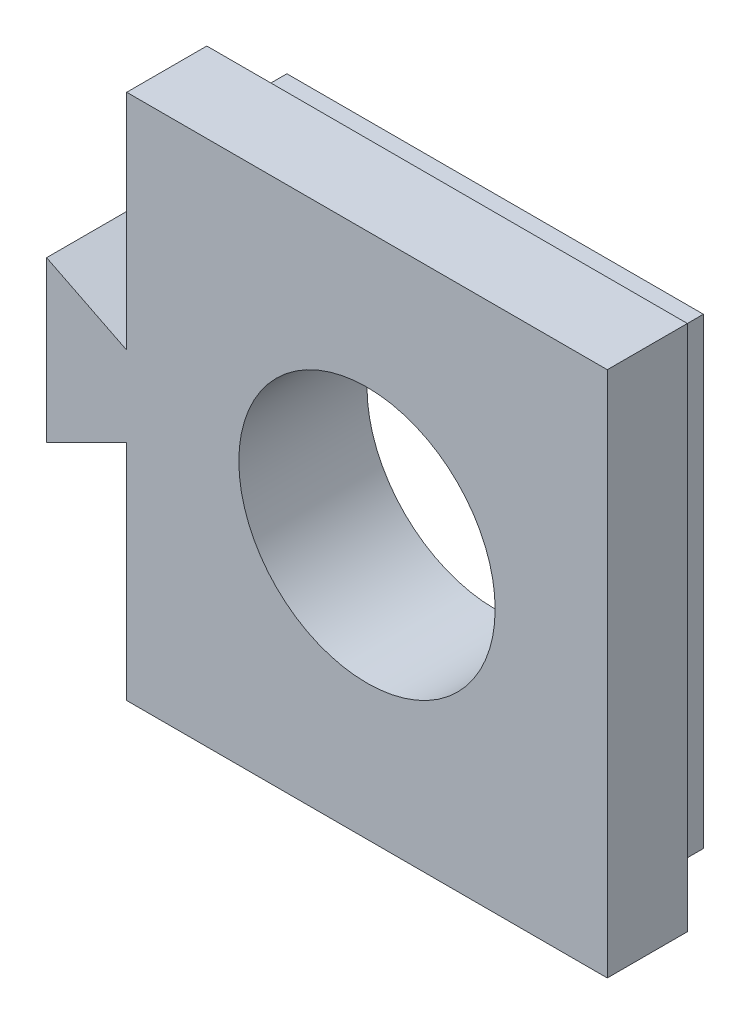
SolidWorks part; units mm, degrees
ref_plane "Alzado" through (0, 0, 0) normal (0, 0, 1) x (1, 0, 0)
ref_plane "Planta" through (0, 0, 0) normal (0, 1, 0) x (1, 0, 0)
ref_plane "Vista lateral" through (0, 0, 0) normal (1, 0, 0) x (0, 0, -1)
sketch "Croquis1" plane through (0, 0, 0) normal (0, 0, 1) x (1, 0, 0)
  line L1 (-2, -5.2848) -> (24, -5.2848)
  line L2 (-2, -5.2848) -> (-2, 23.6)
  line L3 (-2, 23.6) -> (24, 23.6)
  line L4 (24, -5.2848) -> (24, 23.6)
  circle A0 centre (11, 9.1576) radius 8
extrude "Saliente-Extruir1" add sketch "Croquis1" along normal blind 3
sketch "Croquis2" plane through (0, 0, 3) normal (0, 0, 1) x (1, 0, 0)
  line L8 (-4, 25.6) -> (-4, -7.2848)
  line L9 (26, 25.6) -> (-4, 25.6)
  line L10 (26, -7.2848) -> (26, 25.6)
  line L11 (-4, -7.2848) -> (26, -7.2848)
  line L12 (-4, 25.6) -> (-4, -7.2848)
  line L13 (26, 25.6) -> (-4, 25.6)
  line L14 (26, -7.2848) -> (26, 25.6)
  line L15 (-4, -7.2848) -> (26, -7.2848)
  dimension "D1" = 2
extrude "Saliente-Extruir2" add sketch "Croquis2" along normal blind 5
sketch "Croquis4" plane through (0, 0, 8) normal (0, 0, 1) x (1, 0, 0)
  line L0 (-4, 9.1576) -> (-9, 9.1576) construction
  line L1 (-4, 25.6) -> (-4, -7.2848) construction
  line L2 (-9, 9.1576) -> (-9, 4.1576) construction
  line L3 (-4, 9.1576) -> (-4, 6.6576) construction
  line L4 (-9, 14.1576) -> (-9, 4.1576)
  line L5 (-9, 4.1576) -> (-4, 6.6576)
  line L6 (-9, 14.1576) -> (-4, 11.6576)
  line L7 (-4, 11.6576) -> (-4, 6.6576)
extrude "Saliente-Extruir3" add sketch "Croquis4" against normal blind 5
sketch "Croquis5" plane through (0, 0, 3) normal (0, 0, -1) x (-1, 0, 0)
  circle A0 centre (-11, 9.1576) radius 8
extrude "Cortar-Extruir1" cut sketch "Croquis5" against normal blind 10
